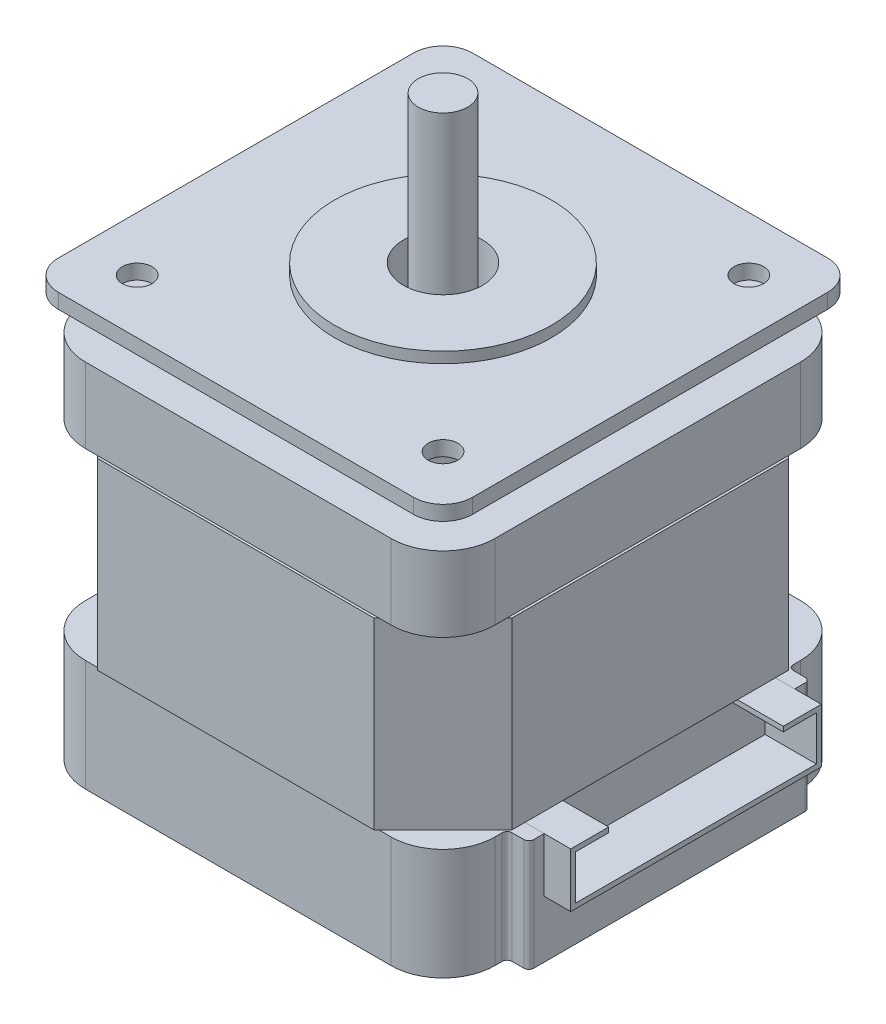
SolidWorks part; units mm, degrees
other "Shaft"
other "MountFlange"
other "Stator"
other "Cap"
other "Plug"
ref_plane "Front Plane" through (0, 0, 0) normal (0, 0, 1) x (1, 0, 0)
ref_plane "Top Plane" through (0, 0, 0) normal (0, 1, 0) x (1, 0, 0)
ref_plane "Right Plane" through (0, 0, 0) normal (1, 0, 0) x (0, 0, -1)
sketch "Sketch1" plane through (0, 0, 0) normal (0, 1, 0) x (1, 0, 0)
  line L1 (-20.75, 20.75) -> (20.75, 20.75)
  line L2 (-20.75, 20.75) -> (-20.75, -20.75)
  line L3 (-20.75, -20.75) -> (20.75, -20.75)
  line L4 (20.75, 20.75) -> (20.75, -20.75)
  line L5 (-20.75, 20.75) -> (20.75, -20.75) construction
  line L6 (-20.75, -20.75) -> (20.75, 20.75) construction
  point P0 (0, 0)
  dimension "D1" = 41.5
extrude "Boss-Extrude1" add sketch "Sketch1" along normal blind 11.3
sketch "Sketch2" plane through (0, 11.3, 0) normal (0, 1, 0) x (1, 0, 0)
  line L1 (-21, 21) -> (21, 21)
  line L2 (-21, 21) -> (-21, -21)
  line L3 (-21, -21) -> (21, -21)
  line L4 (21, 21) -> (21, -21)
  line L5 (-21, 21) -> (21, -21) construction
  line L6 (-21, -21) -> (21, 21) construction
  point P0 (0, 0)
  dimension "D1" = 42
extrude "Boss-Extrude2" add sketch "Sketch2" along normal blind 18.6 separate body
chamfer "Chamfer1" distance 7 angle 45 4 edges at (21, 20.6, 21) (-21, 20.6, 21) (-21, 20.6, -21) (21, 20.6, -21)
sketch "Sketch6" plane through (0, 29.9, 0) normal (0, 1, 0) x (1, 0, 0)
  line L1 (-20.75, 20.75) -> (20.75, 20.75)
  line L2 (-20.75, 20.75) -> (-20.75, -20.75)
  line L3 (-20.75, -20.75) -> (20.75, -20.75)
  line L4 (20.75, 20.75) -> (20.75, -20.75)
  line L5 (-20.75, 20.75) -> (20.75, -20.75) construction
  line L6 (-20.75, -20.75) -> (20.75, 20.75) construction
  point P0 (0, 0)
  dimension "D1" = 41.5
extrude "Boss-Extrude3" add sketch "Sketch6" along normal blind 7.6 separate body
sketch "Sketch7" plane through (0, 37.5, 0) normal (0, 1, 0) x (1, 0, 0)
  circle A0 centre (0, 0) radius 17.5
  dimension "D1" = 35
extrude "Boss-Extrude4" add sketch "Sketch7" along normal blind 3.5
sketch "Sketch8" plane through (0, 41, 0) normal (0, 1, 0) x (1, 0, 0)
  line L1 (21, -21) -> (-21, -21)
  line L2 (21, -21) -> (21, 21)
  line L3 (21, 21) -> (-21, 21)
  line L4 (-21, -21) -> (-21, 21)
  line L5 (21, -21) -> (-21, 21) construction
  line L6 (21, 21) -> (-21, -21) construction
  point P0 (0, 0)
  dimension "D1" = 42
extrude "Boss-Extrude5" add sketch "Sketch8" along normal blind 1.5
fillet "Fillet1" radius 5.25 4 edges at (-20.75, 5.65, 20.75) (-20.75, 5.65, -20.75) (20.75, 5.65, -20.75) (20.75, 5.65, 20.75)
fillet "Fillet2" radius 5.25 4 edges at (20.75, 33.7, 20.75) (-20.75, 33.7, 20.75) (-20.75, 33.7, -20.75) (20.75, 33.7, -20.75)
fillet "Fillet3" radius 3 4 edges at (-21, 41.75, 21) (21, 41.75, 21) (21, 41.75, -21) (-21, 41.75, -21)
sketch "Sketch9" plane through (0, 42.5, 0) normal (0, 1, 0) x (1, 0, 0)
  circle A0 centre (0, 0) radius 11
  dimension "D1" = 22
extrude "Boss-Extrude6" add sketch "Sketch9" along normal blind 1.1
sketch "Sketch4" plane through (0, 0, 0) normal (0, -1, 0) x (1, 0, 0)
  line L1 (-15.5, 15.5) -> (15.5, 15.5) construction
  line L2 (-15.5, 15.5) -> (-15.5, -15.5) construction
  line L3 (-15.5, -15.5) -> (15.5, -15.5) construction
  line L4 (15.5, 15.5) -> (15.5, -15.5) construction
  line L5 (-15.5, 15.5) -> (15.5, -15.5) construction
  line L6 (-15.5, -15.5) -> (15.5, 15.5) construction
  circle A0 centre (-15.5, -15.5) radius 1.5
  circle A1 centre (15.5, -15.5) radius 1.5
  circle A2 centre (15.5, 15.5) radius 1.5
  circle A3 centre (-15.5, 15.5) radius 1.5
  circle A4 centre (0, 0) radius 4
  point P0 (0, 0)
  dimension "D2" = 3
  dimension "D3" = 8
  dimension "D1" = 31
extrude "Cut-Extrude1" cut sketch "Sketch4" against normal through all
ref_plane "Plane1" through (0, 58.5, 0) normal (0, -1, 0) x (-1, 0, 0)
sketch "Sketch10" plane through (0, 58.5, 0) normal (0, -1, 0) x (-1, 0, 0)
  circle A0 centre (0, 0) radius 2.5
  dimension "D1" = 5
extrude "Boss-Extrude7" add sketch "Sketch10" along normal offset from surface (53 mm away) 5.5 separate body up to face at (15.5, 0, -17)
sketch "Sketch11" plane through (20.75, 0, 0) normal (1, 0, 0) x (0, 0, -1)
  line L0 (0, 11.3) -> (0, 0) construction
  line L1 (-15.5, 11.3) -> (15.5, 11.3) construction
  line L2 (-15.5, 0) -> (15.5, 0) construction
  line L4 (-14.25, 11.3) -> (14.25, 11.3)
  line L5 (-14.25, 11.3) -> (-14.25, 0)
  line L6 (-14.25, 0) -> (14.25, 0)
  line L7 (14.25, 11.3) -> (14.25, 0)
  dimension "D1" = 28.5
extrude "Boss-Extrude8" add sketch "Sketch11" along normal offset from surface (2.2 mm away) 43.7 up to face at (-20.75, 5.65, 0)
sketch "Sketch12" plane through (22.95, 0, 0) normal (1, 0, 0) x (0, 0, -1)
  line L0 (0, 11.3) -> (0, 0) construction
  line L1 (14.25, 11.3) -> (-14.25, 11.3) construction
  line L2 (-14.25, 0) -> (14.25, 0) construction
  line L4 (-12.7, 11.3) -> (12.7, 11.3)
  line L5 (-12.7, 11.3) -> (-12.7, 5.8)
  line L6 (-12.7, 5.8) -> (12.7, 5.8)
  line L7 (12.7, 11.3) -> (12.7, 5.8)
  dimension "D1" = 25.4
  dimension "D2" = 5.5
extrude "Cut-Extrude2" cut sketch "Sketch12" against normal blind 3
fillet "Fillet4" radius 0.5 4 edges at (20.75, 5.65, -14.25) (22.95, 5.65, -14.25) (22.95, 5.65, 14.25) (20.75, 5.65, 14.25)
sketch "Sketch13" plane through (19.95, 0, 0) normal (1, 0, 0) x (0, 0, -1)
  line L4 (-12.7, 11.3) -> (-12.7, 5.8)
  line L5 (-12.7, 5.8) -> (12.7, 5.8)
  line L6 (12.7, 5.8) -> (12.7, 11.3)
  line L7 (12.7, 11.3) -> (-12.7, 11.3)
  line L8 (-12.7, 11.3) -> (-12.7, 5.8)
  line L9 (-12.7, 5.8) -> (12.7, 5.8)
  line L10 (12.7, 5.8) -> (12.7, 11.3)
  line L11 (12.7, 11.3) -> (-12.7, 11.3)
  dimension "D1" = 0
extrude "Boss-Extrude9" add sketch "Sketch13" along normal blind 0.5 separate body
sketch "Sketch14" plane through (20.45, 0, 0) normal (1, 0, 0) x (0, 0, -1)
  line L0 (8.85, 11.3) -> (12.7, 11.3)
  line L1 (12.7, 11.3) -> (-12.7, 11.3) construction
  line L2 (12.7, 11.3) -> (12.7, 5.8)
  line L3 (12.7, 5.8) -> (-12.7, 5.8)
  line L4 (-12.7, 5.8) -> (12.7, 5.8) construction
  line L5 (0, 5.8) -> (0, 6.3) construction
  line L6 (-12.2, 6.3) -> (12.2, 6.3)
  line L7 (12.2, 6.3) -> (12.2, 10.8)
  line L8 (12.2, 10.8) -> (8.85, 10.8)
  line L9 (8.85, 10.8) -> (8.85, 11.3)
  line L10 (12.2, 10.8) -> (12.7, 10.8) construction
  line L11 (-12.2, 10.8) -> (-12.7, 10.8) construction
  line L12 (-8.85, 10.8) -> (-8.85, 11.3)
  line L13 (-12.2, 10.8) -> (-8.85, 10.8)
  line L14 (-12.2, 6.3) -> (-12.2, 10.8)
  line L15 (-12.7, 11.3) -> (-12.7, 5.8)
  line L16 (-8.85, 11.3) -> (-12.7, 11.3)
  dimension "D1" = 0.5
  dimension "D2" = 17.7
extrude "Boss-Extrude10" add sketch "Sketch14" along normal offset from surface (5.2 mm away) 46.4 up to face at (-20.75, 5.65, 0)
